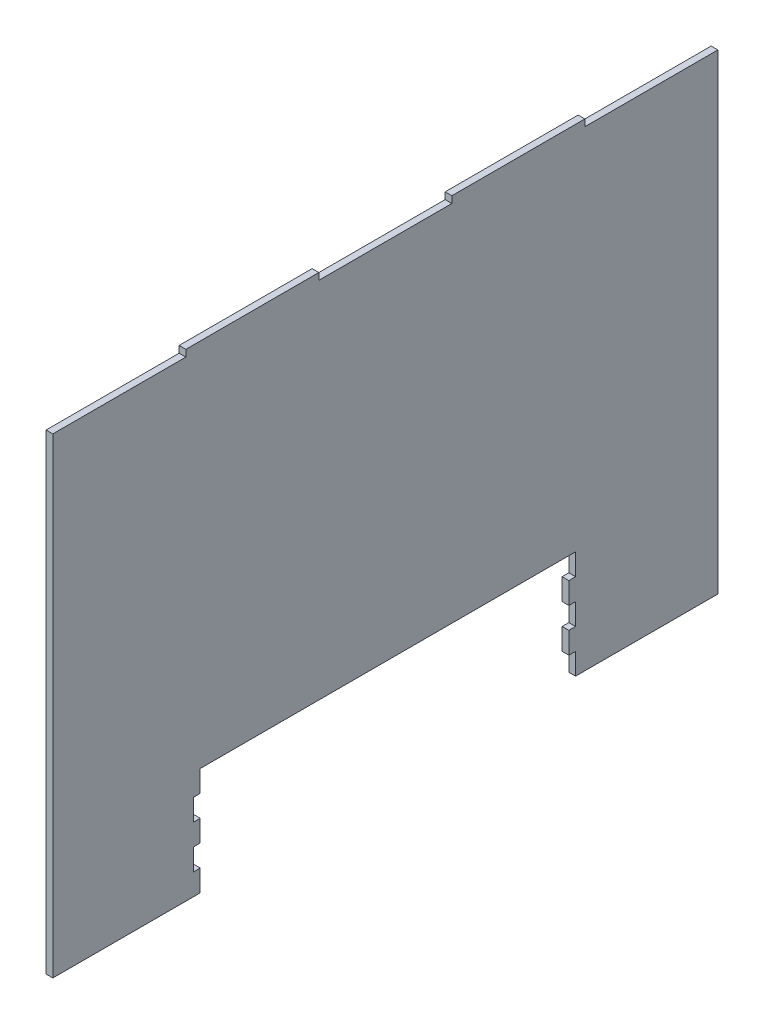
SolidWorks part; units mm, degrees
ref_plane "Front Plane" through (0, 0, 0) normal (0, 0, 1) x (1, 0, 0)
ref_plane "Top Plane" through (0, 0, 0) normal (0, 1, 0) x (1, 0, 0)
ref_plane "Right Plane" through (0, 0, 0) normal (1, 0, 0) x (0, 0, -1)
sketch "Sketch1" plane through (0, 0, 0) normal (1, 0, 0) x (0, 0, -1)
  line L0 (-247, 277.5) -> (-148.2, 277.5)
  line L2 (-247, 277.5) -> (-247, -72.5)
  line L3 (-247, -72.5) -> (-137.5, -72.5)
  line L4 (247, 277.5) -> (247, -72.5)
  line L7 (-148.2, 282.5) -> (-49.4, 282.5)
  line L9 (49.4, 282.5) -> (148.2, 282.5)
  line L11 (-148.2, 282.5) -> (-148.2, 277.5)
  line L12 (-49.4, 282.5) -> (-49.4, 277.5)
  line L13 (49.4, 282.5) -> (49.4, 277.5)
  line L14 (148.2, 282.5) -> (148.2, 277.5)
  line L15 (-49.4, 277.5) -> (49.4, 277.5)
  line L16 (148.2, 277.5) -> (247, 277.5)
  line L17 (-137.5, -72.5) -> (-137.5, -56.5)
  line L18 (0, 7.5) -> (-137.5, 7.5)
  line L19 (-137.5, -40.3593) -> (-137.5, -24.5)
  line L20 (0, 7.5) -> (141.2627, 7.5)
  line L21 (141.2627, 7.5) -> (141.2627, -8.5)
  line L24 (141.2627, -72.5) -> (247, -72.5)
  line L25 (-142.5, -8.5) -> (-142.5, -24.5)
  line L26 (-137.5, -8.5) -> (-137.5, 7.5)
  line L27 (-142.5, -40.5) -> (-142.5, -56.5)
  line L29 (141.2627, -24.5) -> (141.2627, -40.5)
  line L31 (141.2627, -56.5) -> (141.2627, -72.5)
  line L33 (136.2627, -56.5) -> (136.2627, -40.5)
  line L35 (136.2627, -24.5) -> (136.2627, -8.5)
  line L37 (-142.5, -8.5) -> (-137.5, -8.5)
  line L38 (-142.5, -24.5) -> (-137.5, -24.5)
  line L39 (-142.5, -40.5) -> (-137.5, -40.3593)
  line L40 (-142.5, -56.5) -> (-137.5, -56.5)
  line L45 (136.2627, -8.5) -> (141.2627, -8.5)
  line L46 (136.2627, -24.5) -> (141.2627, -24.5)
  line L47 (136.2627, -40.5) -> (141.2627, -40.5)
  line L48 (136.2627, -56.5) -> (141.2627, -56.5)
  point P0 (0, 0)
  dimension "D1" = 350
extrude "Boss-Extrude1" add sketch "Sketch1" along normal blind 5
